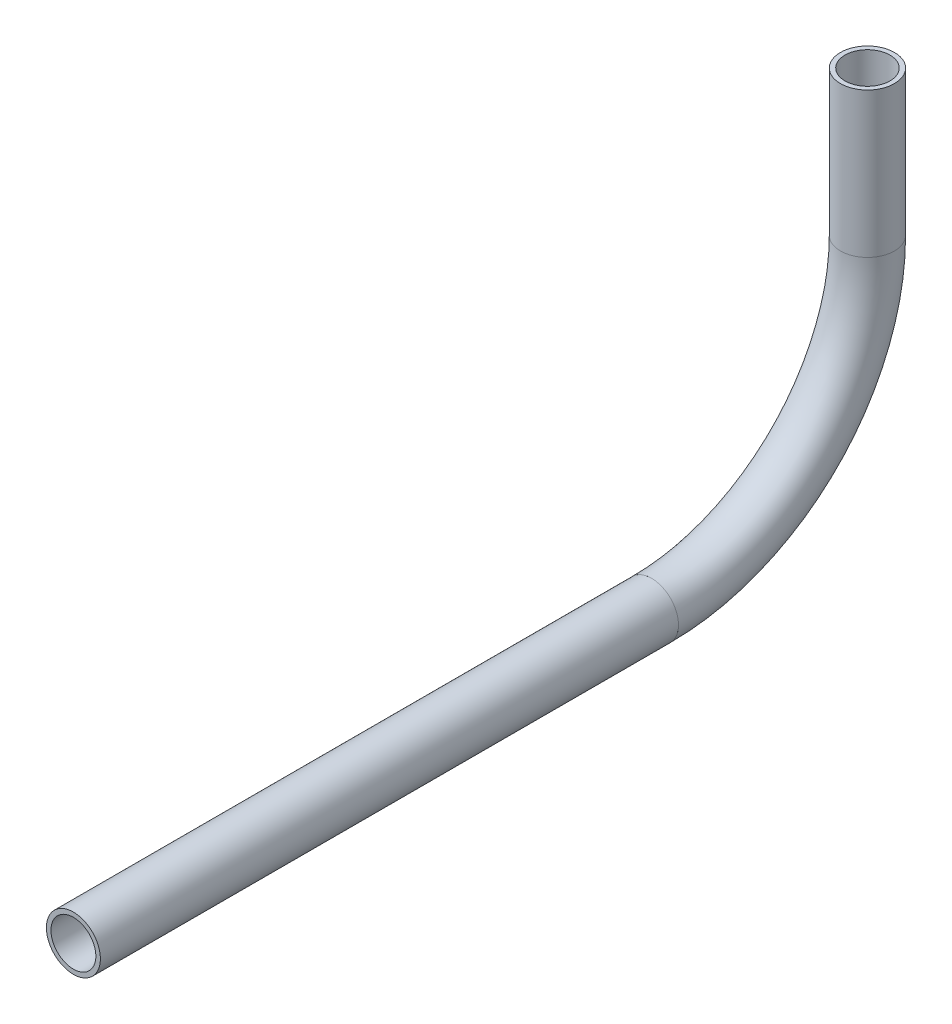
SolidWorks part; units mm, degrees
ref_plane "Front Plane" through (0, 0, 0) normal (0, 0, 1) x (1, 0, 0)
ref_plane "Top Plane" through (0, 0, 0) normal (0, 1, 0) x (1, 0, 0)
ref_plane "Right Plane" through (0, 0, 0) normal (1, 0, 0) x (0, 0, -1)
sketch "Sketch1" plane through (0, 0, 0) normal (1, 0, 0) x (0, 0, -1)
  line L0 (-303.1646, 599.96) -> (-167.159, 599.96)
  line L1 (-116.359, 650.76) -> (-116.359, 684.869)
  arc A0 (-167.159, 599.96) -> (-116.359, 650.76) centre (-167.159, 650.76) ccw
  point P2 (-115.8977, 670.2244)
  point P6 (0, 0)
  point P7 (-116.359, 684.869)
  dimension "D1" = 50.8
other "Pipe 0.5 SCH 40(1)"
ref_plane "Plane1" through (0, 599.96, 303.1646) normal (0, 0, -1) x (0, 1, 0)
sketch "Sketch11" plane through (0, 599.96, 303.1646) normal (0, 0, -1) x (0, 1, 0)
  circle A0 centre (0, 0) radius 5.2832
  circle A1 centre (0, 0) radius 6.35
  point P5 (0, 0)
  dimension "In_dia" = 10.5664
  dimension "Out_dia" = 12.7
